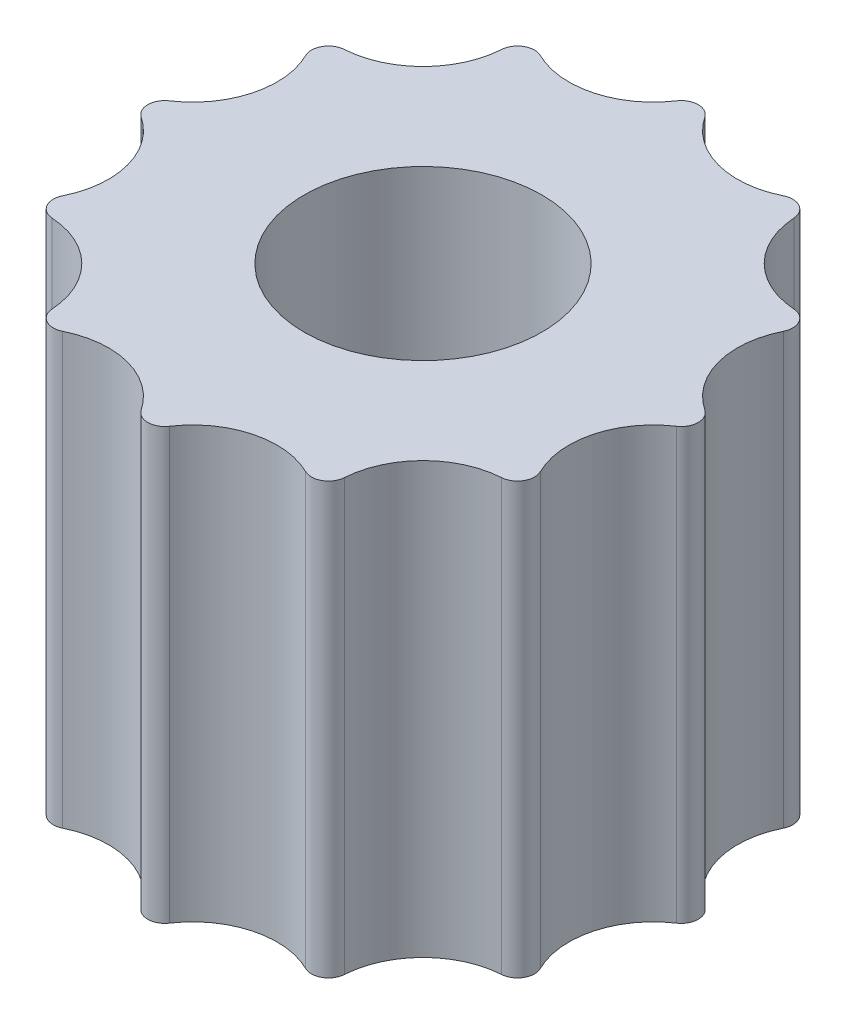
SolidWorks part; units mm, degrees
ref_plane "前视基准面" through (0, 0, 0) normal (0, 0, 1) x (1, 0, 0)
ref_plane "上视基准面" through (0, 0, 0) normal (0, 1, 0) x (1, 0, 0)
ref_plane "右视基准面" through (0, 0, 0) normal (1, 0, 0) x (0, 0, -1)
other "Configuration Table"
sketch "草图1" plane through (0, 0, 0) normal (0, 1, 0) x (1, 0, 0)
  line L0 (0, 0) -> (0, 2.7302) construction
  line L1 (0, 5) -> (-4.3301, 2.5) construction
  line L2 (-4.3301, 2.5) -> (-4.3301, -2.5) construction
  line L3 (-4.3301, -2.5) -> (0, -5) construction
  line L4 (0, -5) -> (4.3301, -2.5) construction
  line L5 (4.3301, -2.5) -> (4.3301, 2.5) construction
  line L6 (4.3301, 2.5) -> (0, 5) construction
  line L7 (0, 0) -> (-2.7003, 4.677) construction
  line L8 (0, 0) -> (-4.3301, 2.5) construction
  circle A0 centre (0, 0) radius 5 construction
  circle A1 centre (0, 0) radius 4.3301 construction
  circle A2 centre (0, 0) radius 2.1
  circle A3 centre (0, 0) radius 5.5 construction
  arc A4 (-2.75, 4.7631) -> (0, 5.5) centre (-1.4882, 5.5541) ccw
  arc A5 (-4.7631, 2.75) -> (-2.75, 4.7631) centre (-4.0659, 4.0659) ccw
  circle A6 centre (0, 0) radius 5.75 construction
  arc A7 (2.75, 4.7631) -> (4.7631, 2.75) centre (4.0659, 4.0659) ccw
  arc A8 (0, 5.5) -> (2.75, 4.7631) centre (1.4882, 5.5541) ccw
  arc A9 (5.5, 0) -> (4.7631, -2.75) centre (5.5541, -1.4882) ccw
  arc A10 (4.7631, 2.75) -> (5.5, 0) centre (5.5541, 1.4882) ccw
  arc A11 (2.75, -4.7631) -> (0, -5.5) centre (1.4882, -5.5541) ccw
  arc A12 (4.7631, -2.75) -> (2.75, -4.7631) centre (4.0659, -4.0659) ccw
  arc A13 (-2.75, -4.7631) -> (-4.7631, -2.75) centre (-4.0659, -4.0659) ccw
  arc A14 (0, -5.5) -> (-2.75, -4.7631) centre (-1.4882, -5.5541) ccw
  arc A15 (-5.5, 0) -> (-4.7631, 2.75) centre (-5.5541, 1.4882) ccw
  arc A16 (-4.7631, -2.75) -> (-5.5, 0) centre (-5.5541, -1.4882) ccw
  point P47 (0, 0)
  dimension "D1" = 10
  dimension "D2" = 4.2
  dimension "D3" = 11
  dimension "D4" = 30
  dimension "D5" = 11.5
  dimension "D6" = 6
extrude "凸台-拉伸1" add sketch "草图1" along normal blind 7.6
fillet "圆角1" radius 0.3 12 edges at (4.7631, 3.8, -2.75) (5.5, 3.8, 0) (4.7631, 3.8, 2.75) (2.75, 3.8, 4.7631) (0, 3.8, 5.5) (-2.75, 3.8, 4.7631) (-4.7631, 3.8, 2.75) (-5.5, 3.8, 0) (-4.7631, 3.8, -2.75) (-2.75, 3.8, -4.7631) (0, 3.8, -5.5) (2.75, 3.8, -4.7631)
